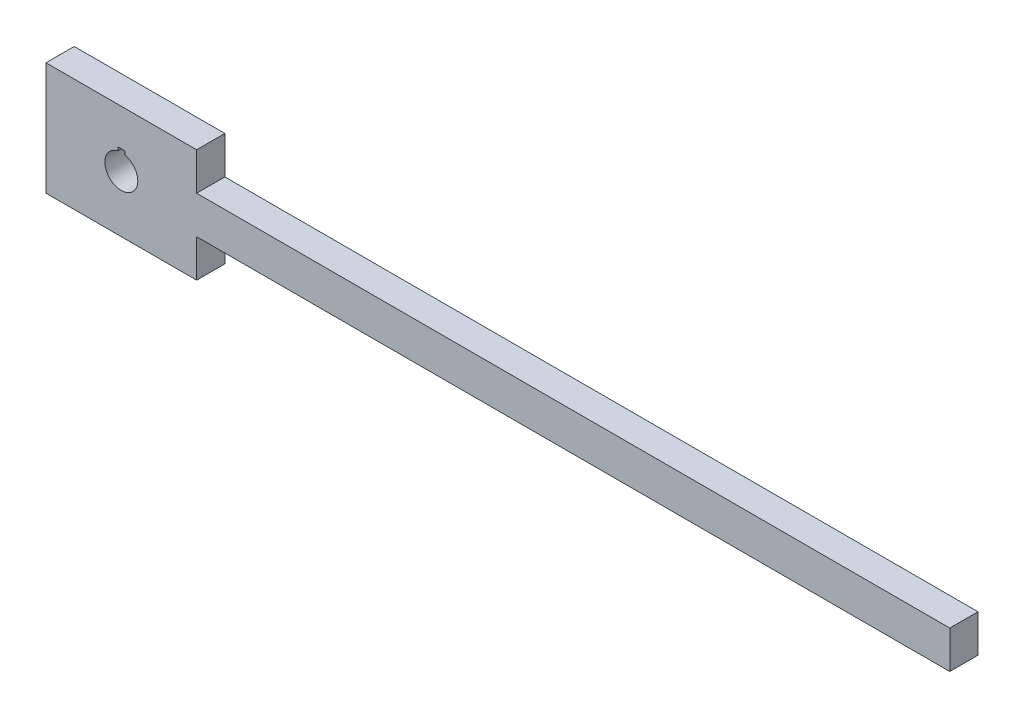
SolidWorks part; units mm, degrees
ref_plane "Front Plane" through (0, 0, 0) normal (0, 0, 1) x (1, 0, 0)
ref_plane "Top Plane" through (0, 0, 0) normal (0, 1, 0) x (1, 0, 0)
ref_plane "Right Plane" through (0, 0, 0) normal (1, 0, 0) x (0, 0, -1)
sketch "Sketch1" plane through (0, 0, 0) normal (0, 0, 1) x (1, 0, 0)
  line L0 (-65.2162, 23.3405) -> (-65.2162, -52.8595)
  line L1 (-65.2162, -52.8595) -> (36.3838, -52.8595)
  line L2 (36.3838, -52.8595) -> (36.3838, -27.4595)
  line L3 (36.3838, -27.4595) -> (544.3838, -27.4595)
  line L4 (544.3838, -27.4595) -> (544.3838, -2.0595)
  line L5 (544.3838, -2.0595) -> (36.3838, -2.0595)
  line L6 (36.3838, -2.0595) -> (36.3838, 23.3405)
  line L7 (36.3838, 23.3405) -> (-65.2162, 23.3405)
  line L8 (36.3838, -14.7595) -> (-65.2162, -14.7595) construction
  line L9 (-14.4162, 23.3405) -> (-14.4162, -52.8595) construction
  dimension "D1" = 76.2
  dimension "D2" = 101.6
  dimension "D3" = 101.6
  dimension "D4" = 25.4
  dimension "D5" = 25.4
  dimension "D6" = 76.2
  dimension "D7" = 25.4
  dimension "D8" = 508
extrude "Boss-Extrude1" add sketch "Sketch1" along normal blind 19.05
sketch "Sketch2" plane through (0, 0, 19.05) normal (0, 0, 1) x (1, 0, 0)
  line L0 (-65.2162, 23.3405) -> (-65.2162, -52.8595) construction
  line L1 (36.3838, 23.3405) -> (-65.2162, 23.3405) construction
  line L5 (-12.0376, -3.9045) -> (-12.0381, -1.5245)
  line L8 (-12.0381, -1.5245) -> (-16.8006, -1.5245)
  line L9 (-16.8006, -3.9058) -> (-16.8006, -1.5245)
  arc A0 (-16.8006, -3.9058) -> (-12.0376, -3.9045) centre (-14.4162, -14.7595) ccw
  point P11 (-14.4162, -14.7595)
  point P17 (0, 0)
  dimension "D1" = 22.225
  dimension "D2" = 4.7625
  dimension "D3" = 2.3812
  dimension "D4" = 50.8
  dimension "D5" = 38.1
  dimension "D6" = 13.2349
  dimension "D7" = 2.3813
extrude "Cut-Extrude1" cut sketch "Sketch2" against normal through all
